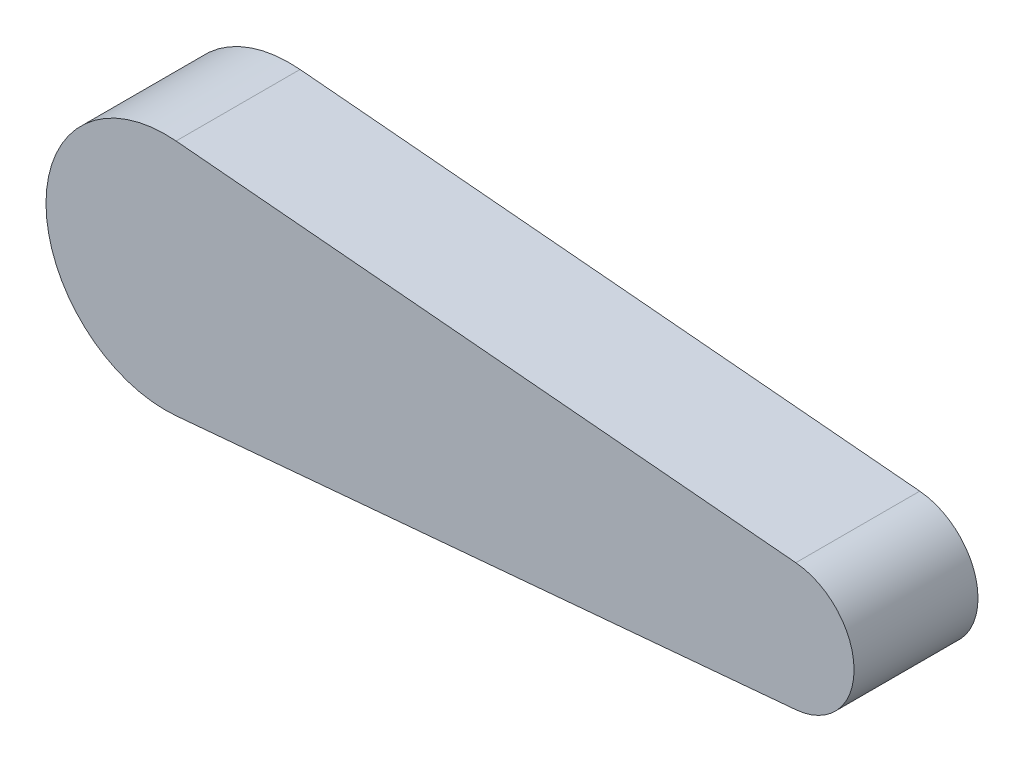
SolidWorks part; units mm, degrees
material "ABS"
ref_plane "Plan de face" through (0, 0, 0) normal (0, 0, 1) x (1, 0, 0)
ref_plane "Plan de dessus" through (0, 0, 0) normal (0, 1, 0) x (1, 0, 0)
ref_plane "Plan de droite" through (0, 0, 0) normal (1, 0, 0) x (0, 0, -1)
sketch "Esquisse1" plane through (0, 0, 0) normal (0, 0, 1) x (1, 0, 0)
  line L0 (0.1658, 0) -> (55.1658, 0) construction
  line L1 (10.4953, 9.6) -> (60.4953, 5.1357)
  line L2 (10.4953, -9.6) -> (60.4953, -5.1357)
  arc A0 (10.4953, 9.6) -> (10.4953, -9.6) centre (9.6382, 0) ccw
  arc A1 (60.4953, 5.1357) -> (60.4953, -5.1357) centre (60.0368, 0) cw
  dimension "D1" = 9.6
  dimension "D2" = 55
  dimension "D3" = 5.1357
  dimension "D4" = 50
extrude "Boss.-Extru.1" add sketch "Esquisse1" along normal blind 10
sketch "Sketch1" plane through (0, 0, 0) normal (0, 0, -1) x (-1, 0, 0)
  line L0 (0, 0) -> (-65.1929, 0) construction
  line L1 (-10.4953, 9.6) -> (-10.4953, -9.6) construction
  arc A0 (-60.4953, 5.1357) -> (-60.4953, -5.1357) centre (-60.0368, 0) ccw construction
  circle A1 centre (-10.4953, 0) radius 3.95
  dimension "D1" = 7.9
extrude "Cut-Extrude1" cut sketch "Sketch1" against normal blind 8
